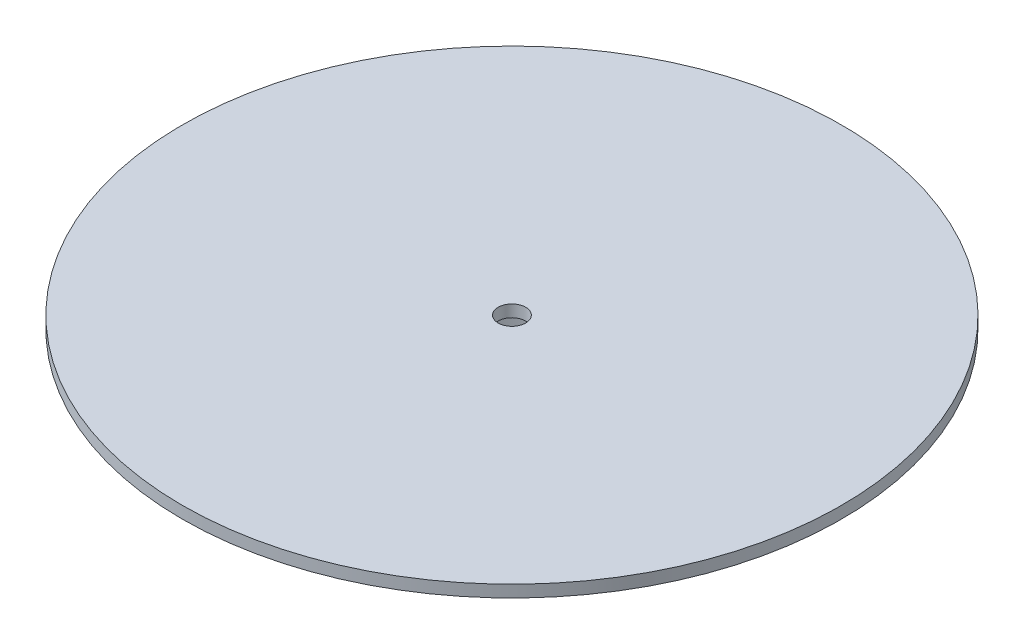
SolidWorks part; units mm, degrees
material "ABS"
ref_plane "Front Plane" through (0, 0, 0) normal (0, 0, 1) x (1, 0, 0)
ref_plane "Top Plane" through (0, 0, 0) normal (0, 1, 0) x (1, 0, 0)
ref_plane "Right Plane" through (0, 0, 0) normal (1, 0, 0) x (0, 0, -1)
sketch "Sketch1" plane through (0, 0, 0) normal (0, 1, 0) x (1, 0, 0)
  circle A0 centre (0, 0) radius 76.2
extrude "Boss-Extrude1" add sketch "Sketch1" along normal blind 2.7661
sketch "Sketch4" plane through (0, 0, 0) normal (0, -1, 0) x (1, 0, 0)
  circle A0 centre (0, 0) radius 22.352
  circle A1 centre (0, 0) radius 23.735
  dimension "D1" = 44.704
  dimension "D2" = 47.4701
extrude "Boss-Extrude3" add sketch "Sketch4" along normal blind 35.56
sketch "Sketch5" plane through (0, 0, 0) normal (0, -1, 0) x (1, 0, 0)
  circle A0 centre (0, 0) radius 3.175
extrude "Cut-Extrude1" cut sketch "Sketch5" against normal through all
